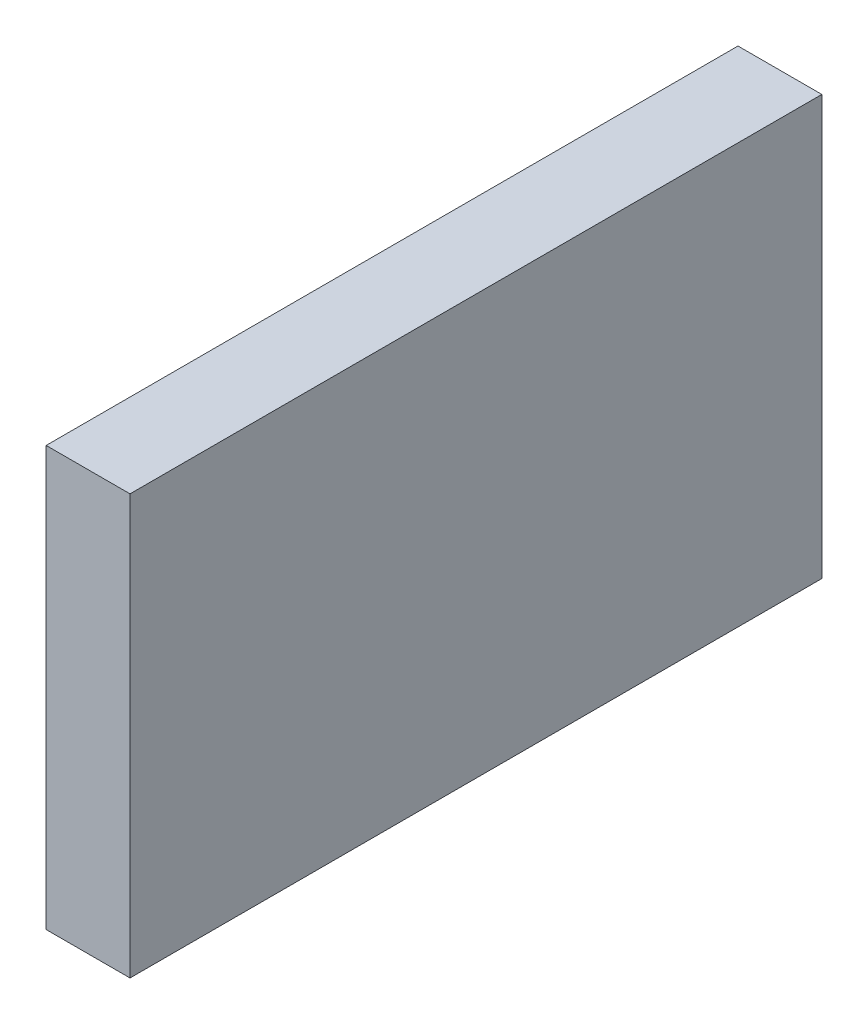
SolidWorks part; units mm, degrees
ref_plane "Alzado" through (0, 0, 0) normal (0, 0, 1) x (1, 0, 0)
ref_plane "Planta" through (0, 0, 0) normal (0, 1, 0) x (1, 0, 0)
ref_plane "Vista lateral" through (0, 0, 0) normal (1, 0, 0) x (0, 0, -1)
sketch "Croquis1" plane through (0, 0, 0) normal (1, 0, 0) x (0, 0, -1)
  line L1 (-16.5, -10) -> (16.5, -10)
  line L2 (-16.5, -10) -> (-16.5, 10)
  line L3 (-16.5, 10) -> (16.5, 10)
  line L4 (16.5, -10) -> (16.5, 10)
  line L5 (-16.5, -10) -> (16.5, 10) construction
  line L6 (-16.5, 10) -> (16.5, -10) construction
  point P0 (0, 0)
  dimension "D1" = 33
  dimension "D2" = 20
extrude "Saliente-Extruir1" add sketch "Croquis1" along normal blind 4
